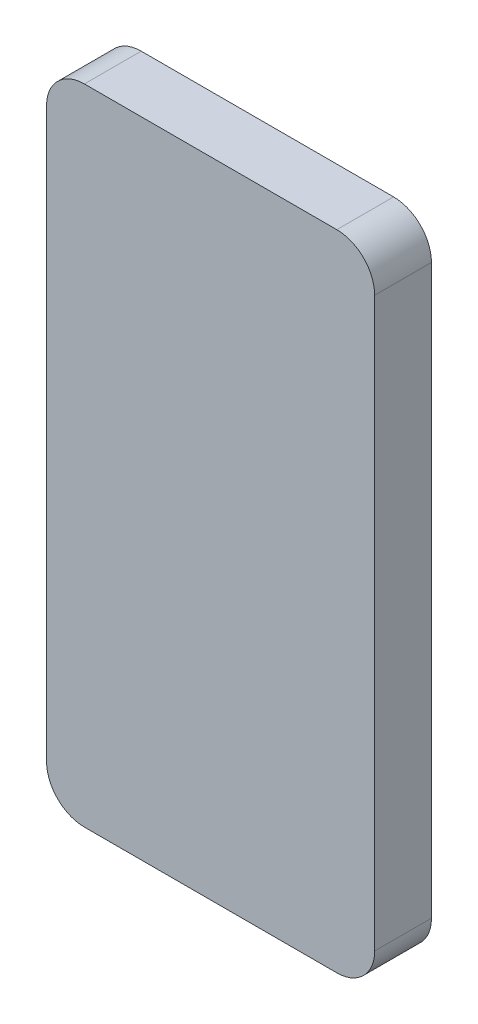
SolidWorks part; units mm, degrees
ref_plane "Front Plane" through (0, 0, 0) normal (0, 0, 1) x (1, 0, 0)
ref_plane "Top Plane" through (0, 0, 0) normal (0, 1, 0) x (1, 0, 0)
ref_plane "Right Plane" through (0, 0, 0) normal (1, 0, 0) x (0, 0, -1)
sketch "Sketch1" plane through (0, 0, 0) normal (0, 0, 1) x (1, 0, 0)
  line L1 (-33.02, 64.77) -> (33.02, 64.77)
  line L2 (-33.02, 64.77) -> (-33.02, -64.77)
  line L3 (-33.02, -64.77) -> (33.02, -64.77)
  line L4 (33.02, 64.77) -> (33.02, -64.77)
  line L5 (-33.02, 64.77) -> (33.02, -64.77) construction
  line L6 (-33.02, -64.77) -> (33.02, 64.77) construction
  point P0 (0, 0)
  dimension "D1" = 66.04
  dimension "D2" = 129.54
extrude "Boss-Extrude1" add sketch "Sketch1" along normal blind 11.43
fillet "Fillet1" radius 7.62 4 edges at (-33.02, -64.77, 5.715) (33.02, -64.77, 5.715) (-33.02, 64.77, 5.715) (33.02, 64.77, 5.715)
